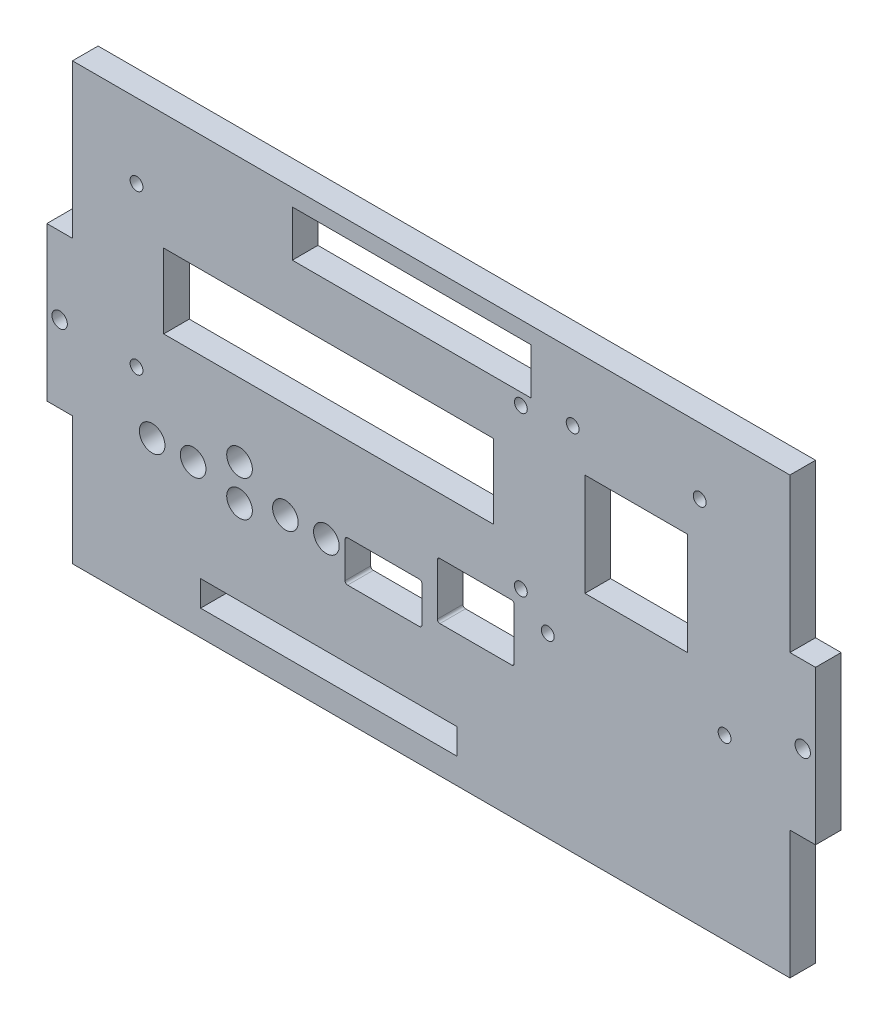
SolidWorks part; units mm, degrees
ref_plane "Front Plane" through (0, 0, 0) normal (0, 0, 1) x (1, 0, 0)
ref_plane "Top Plane" through (0, 0, 0) normal (0, 1, 0) x (1, 0, 0)
ref_plane "Right Plane" through (0, 0, 0) normal (1, 0, 0) x (0, 0, -1)
sketch "Sketch1" plane through (0, 0, 0) normal (0, 0, 1) x (1, 0, 0)
  line L0 (0, 47.2557) -> (0, -1078.3889) construction
  line L1 (-73.3854, 0) -> (102.8507, 0) construction
  line L2 (-75, -15) -> (-70, -15)
  line L3 (-75, 15) -> (-70, 15)
  line L4 (-70, 45) -> (-70, 15)
  line L5 (70, 45) -> (70, 15)
  line L6 (-75, 15) -> (-75, -15)
  line L7 (75, 15) -> (75, -15)
  line L8 (-70, -40) -> (70, -40)
  line L9 (-70, 45) -> (70, 45)
  line L10 (-70, -15) -> (-70, -40)
  line L11 (70, -15) -> (70, -40)
  line L12 (70, 15) -> (75, 15)
  line L13 (70, -15) -> (75, -15)
  dimension "D1" = 70
  dimension "D2" = 75
  dimension "D3" = 70
  dimension "D4" = 15
  dimension "D5" = 45
  dimension "D6" = 15
  dimension "D7" = 25
extrude "Boss-Extrude1" add sketch "Sketch1" along normal blind 5
sketch "Sketch2" plane through (0, 0, 5) normal (0, 0, 1) x (1, 0, 0)
  line L0 (70, 45) -> (-70, 45) construction
  line L1 (-52.2, 22.255) -> (12.2, 22.255)
  line L2 (-52.2, 22.255) -> (-52.2, 7.745)
  line L3 (-52.2, 7.745) -> (12.2, 7.745)
  line L4 (12.2, 22.255) -> (12.2, 7.745)
  line L5 (-52.2, 22.255) -> (12.2, 7.745) construction
  line L6 (-52.2, 7.745) -> (12.2, 22.255) construction
  line L7 (22.75, -5.3677) -> (57.25, -5.3677) construction
  line L8 (-57.5, 30.5) -> (17.5, 30.5) construction
  line L9 (-57.5, 30.5) -> (-57.5, -0.5) construction
  line L10 (-57.5, -0.5) -> (17.5, -0.5) construction
  line L11 (17.5, 30.5) -> (17.5, -0.5) construction
  line L12 (-57.5, 30.5) -> (17.5, -0.5) construction
  line L13 (-57.5, -0.5) -> (17.5, 30.5) construction
  line L14 (30, 25) -> (50, 25)
  line L15 (30, 25) -> (30, 5)
  line L16 (30, 5) -> (50, 5)
  line L17 (50, 25) -> (50, 5)
  line L18 (30, 25) -> (50, 5) construction
  line L19 (30, 5) -> (50, 25) construction
  line L20 (27.6, 32.1323) -> (52.4, 32.1323) construction
  line L21 (40, 32.1323) -> (40, -42.8677) construction
  circle A0 centre (-57.5, 30.5) radius 1.25
  circle A1 centre (17.5, 30.5) radius 1.25
  circle A2 centre (17.5, -0.5) radius 1.25
  circle A3 centre (-57.5, -0.5) radius 1.25
  circle A4 centre (27.6, 32.1323) radius 1.25
  circle A5 centre (52.4, 32.1323) radius 1.25
  circle A6 centre (22.75, -5.3677) radius 1.25
  circle A7 centre (57.25, -5.3677) radius 1.25
  point P0 (-20, 15)
  point P9 (0, 45)
  point P10 (-20, 15)
  point P17 (40, 15)
  point P32 (40, -5.3677)
  dimension "D7" = 2.5
  dimension "D8" = 2.5
  dimension "D9" = 20
  dimension "D12" = 2.5
  dimension "D13" = 2.5
  dimension "D14" = 2.5
  dimension "D15" = 2.5
  dimension "D16" = 34.5
  dimension "D1" = 14.51
  dimension "D2" = 64.4
  dimension "D3" = 20
  dimension "D4" = 30
  dimension "D5" = 31
  dimension "D6" = 75
  dimension "D10" = 60
  dimension "D11" = 30
  dimension "D17" = 37.5
  dimension "D18" = 17.1323
  dimension "D19" = 24.8
extrude "Cut-Extrude1" cut sketch "Sketch2" against normal blind 5
sketch "Sketch3" plane through (0, 0, 5) normal (0, 0, 1) x (1, 0, 0)
  line L0 (12.2, 22.255) -> (-52.2, 22.255) construction
  line L1 (-27.1, 41.755) -> (19.5, 41.755)
  line L2 (-27.1, 41.755) -> (-27.1, 32.755)
  line L3 (-27.1, 32.755) -> (19.5, 32.755)
  line L4 (19.5, 41.755) -> (19.5, 32.755)
  line L5 (-27.1, 41.755) -> (19.5, 32.755) construction
  line L6 (-27.1, 32.755) -> (19.5, 41.755) construction
  line L7 (12.2, 7.745) -> (12.2, 22.255) construction
  line L8 (-49.4423, -11) -> (-2.3793, -11) construction
  line L10 (72.5, 15) -> (72.5, -15) construction
  line L11 (75, 15) -> (70, 15) construction
  line L12 (70, -15) -> (75, -15) construction
  line L13 (0, -48.5767) -> (0, 50.7624) construction
  line L14 (-72.5, 15) -> (-72.5, -15) construction
  line L15 (-70, 15) -> (-75, 15) construction
  line L16 (-75, -15) -> (-70, -15) construction
  line L17 (-37.4, 5.6907) -> (-37.4, -27.7279) construction
  line L18 (-52.2, 7.745) -> (12.2, 7.745) construction
  line L19 (-16.8, -8.755) -> (-1.8, -8.755)
  line L20 (-16.8, -8.755) -> (-16.8, -16.755)
  line L21 (-16.8, -16.755) -> (-1.8, -16.755)
  line L22 (-1.8, -8.755) -> (-1.8, -16.755)
  line L23 (-16.8, -8.755) -> (-1.8, -16.755) construction
  line L24 (-16.8, -16.755) -> (-1.8, -8.755) construction
  line L25 (1.2, -14.255) -> (16.2, -14.255)
  line L26 (1.2, -14.255) -> (1.2, -3.255)
  line L27 (1.2, -3.255) -> (16.2, -3.255)
  line L28 (16.2, -14.255) -> (16.2, -3.255)
  line L29 (1.2, -14.255) -> (16.2, -3.255) construction
  line L30 (1.2, -3.255) -> (16.2, -14.255) construction
  line L31 (-20, 7.745) -> (-20, -72.745) construction
  line L32 (5, -30) -> (-45, -30)
  line L33 (5, -30) -> (5, -35)
  line L34 (5, -35) -> (-45, -35)
  line L35 (-45, -30) -> (-45, -35)
  line L36 (5, -30) -> (-45, -35) construction
  line L37 (5, -35) -> (-45, -30) construction
  line L38 (-70, -40) -> (70, -40) construction
  circle A0 centre (-54.45, -11) radius 2.5
  circle A1 centre (-46.45, -11) radius 2.5
  circle A2 centre (-37.4, -6.5) radius 2.5
  circle A3 centre (-28.45, -11) radius 2.5
  circle A4 centre (-20.45, -11) radius 2.5
  circle A5 centre (72.5, 0) radius 1.5
  circle A6 centre (-72.5, 0) radius 1.5
  circle A7 centre (-57.5, -0.5) radius 1.25 construction
  circle A8 centre (-37.4, -13.5) radius 2.5
  point P0 (-3.8, 37.255)
  point P7 (12.2, 15)
  point P47 (-9.3, -12.755)
  point P52 (8.7, -8.755)
  point P59 (-20, -32.5)
  dimension "D5" = 5
  dimension "D6" = 8
  dimension "D11" = 3
  dimension "D10" = 10.5
  dimension "D7" = 9.05
  dimension "D1" = 9
  dimension "D2" = 46.6
  dimension "D3" = 15
  dimension "D4" = 16
  dimension "D8" = 4.5
  dimension "D9" = 8
  dimension "D12" = 11.05
  dimension "D13" = 2.5
  dimension "D14" = 8.95
  dimension "D15" = 8
  dimension "D16" = 15
  dimension "D17" = 11
  dimension "D18" = 15
  dimension "D19" = 18
  dimension "D20" = 4
  dimension "D21" = 11
  dimension "D22" = 4
  dimension "D23" = 5
  dimension "D24" = 50
  dimension "D25" = 5
extrude "Cut-Extrude2" cut sketch "Sketch3" against normal blind 10
fillet "Fillet1" radius 0.5 8 edges at (-16.8, -16.755, 2.5) (-16.8, -8.755, 2.5) (-1.8, -16.755, 2.5) (-1.8, -8.755, 2.5) (1.2, -14.255, 2.5) (16.2, -14.255, 2.5) (16.2, -3.255, 2.5) (1.2, -3.255, 2.5)
